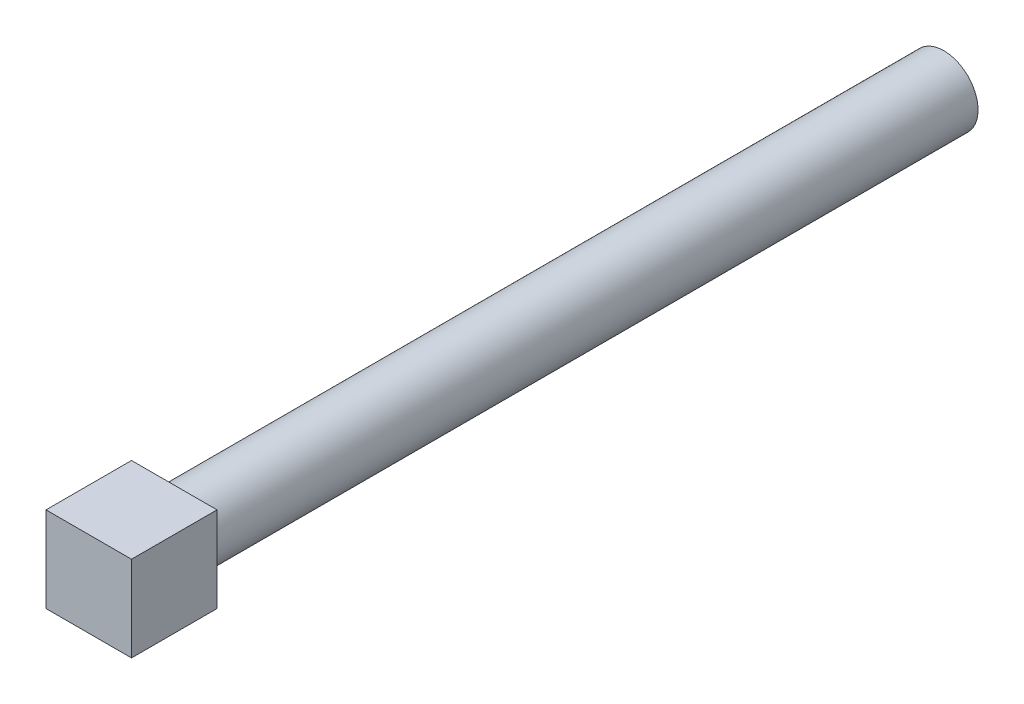
SolidWorks part; units mm, degrees
ref_plane "Front" through (0, 0, 0) normal (0, 0, 1) x (1, 0, 0)
ref_plane "Top" through (0, 0, 0) normal (0, 1, 0) x (1, 0, 0)
ref_plane "Right" through (0, 0, 0) normal (1, 0, 0) x (0, 0, -1)
sketch "草图1" plane through (0, 0, 0) normal (0, 0, 1) x (1, 0, 0)
  line L1 (-5, 5) -> (5, 5)
  line L2 (-5, 5) -> (-5, -5)
  line L3 (-5, -5) -> (5, -5)
  line L4 (5, 5) -> (5, -5)
  dimension "D1" = 10
  dimension "D2" = 10
  dimension "D3" = 5
  dimension "D4" = 5
extrude "凸台-拉伸1" add sketch "草图1" along normal blind 10
sketch "草图2" plane through (0, 0, 0) normal (0, 0, -1) x (-1, 0, 0)
  circle A0 centre (0, 0) radius 4
extrude "凸台-拉伸2" add sketch "草图2" along normal blind 90
